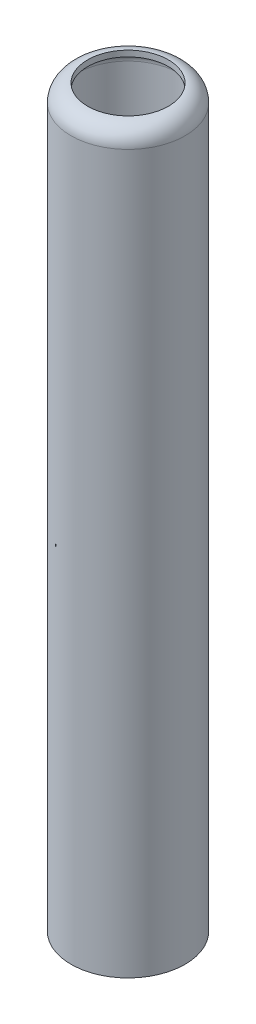
SolidWorks part; units mm, degrees
other "DetailItem1"
material "6061-T6 (SS)"
ref_plane "Front Plane" through (0, 0, 0) normal (0, 0, 1) x (1, 0, 0)
ref_plane "Top Plane" through (0, 0, 0) normal (0, 1, 0) x (1, 0, 0)
ref_plane "Right Plane" through (0, 0, 0) normal (1, 0, 0) x (0, 0, -1)
sketch "Sketch1" plane through (0, 0, 0) normal (0, 1, 0) x (1, 0, 0)
  circle A0 centre (0, 0) radius 14.5
  dimension "D1" = 29
extrude "base" add sketch "Sketch1" along normal blind 186.69
fillet "top-fillet" radius 4.3656 1 edges at (0, 186.69, 14.5)
shell "casing-walls" thickness 1.5
sketch "Sketch2" plane through (0, 0, 0) normal (0, 1, 0) x (1, 0, 0)
  circle A0 centre (0, 0) radius 10.25
  dimension "D1" = 20.5
extrude "top-hole" cut sketch "Sketch2" against normal through all both and the other way through all
equation "\"grain_number\"= 3'Number of grains in the motor. NOT VALID FOR XL CASINGS"
equation "\"casing_diameter\" = 29mm'Diameter of the casing"
equation "\"casing_length\"= ( IIF ( \"casing_diameter\" = 24mm , \"grain_number\" * 1.25 + 1.48 , 0 ) + IIF ( \"casing_diameter\" = 29mm , \"grain_number\" * 1.75 + 2.10 , 0 ) + IIF ( \"casing_diameter\" = 38mm , \"grain_number\" * 2.30457 + 2.284 , 0 ) + IIF ( \"casing_diameter\" = 54mm , \"grain_number\" * 3.31 + 2.28 , 0 ) ) * 25.4mm'DO NOT TOUCH"
equation "\"D1@Sketch1\"=\"casing_diameter\""
equation "\"D1@base\" = \"casing_length\""
equation "\"fillet_radius\"= 0.171875in'approximate"
equation "\"wall_thickness\"= 1.5mm'Thickness of the casing walls"
equation "\"D1@top-fillet\" = \"fillet_radius\""
equation "\"D1@casing-walls\" = \"wall_thickness\""
equation "\"top_hole_diameter\"= IIF ( \"casing_diameter\" = 24mm , 13mm , 0 ) + IIF ( \"casing_diameter\" = 29mm , 20.5mm , 0 ) + IIF ( \"casing_diameter\" = 38mm , 27mm , 0 ) + IIF ( \"casing_diameter\" = 54mm , 38.3mm , 0 )'DO NOT TOUCH"
equation "\"D1@Sketch2\"=\"top_hole_diameter\""
equation "\"D1@top-hole\" = \"casing_length\" + 1mm"
